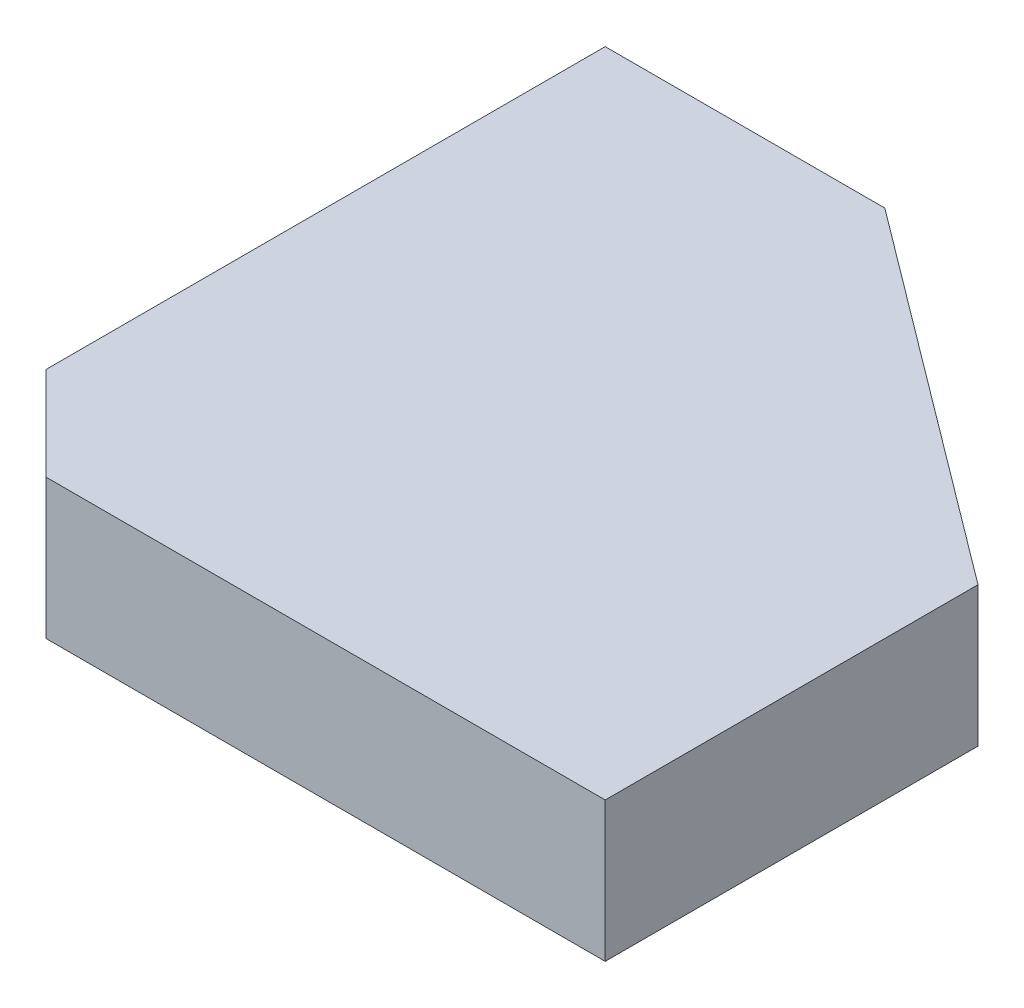
SolidWorks part; units mm, degrees
material "PW20:29:Sc:0:"
ref_plane "Front" through (0, 0, 0) normal (0, 0, 1) x (1, 0, 0)
ref_plane "Top" through (0, 0, 0) normal (0, 1, 0) x (1, 0, 0)
ref_plane "Right" through (0, 0, 0) normal (1, 0, 0) x (0, 0, -1)
sketch "Sketch1" plane through (0, 0, 0) normal (0, 1, 0) x (1, 0, 0)
  line L0 (0, 0) -> (44.45, 0)
  line L1 (0, 0) -> (0, 44.45)
  line L2 (19.05, 44.45) -> (0, 44.45)
  line L3 (44.45, 25.4) -> (44.45, 0)
  line L4 (19.05, 44.45) -> (44.45, 25.4)
  dimension "D1" = 44.45
  dimension "D2" = 44.45
  dimension "D3" = 25.4
  dimension "D4" = 19.05
extrude "Base-Extrude" add sketch "Sketch1" along normal mid plane 9.525
chamfer "Chamfer1" distance 6.35 angle 45 1 edges at (0, 0, 0)
